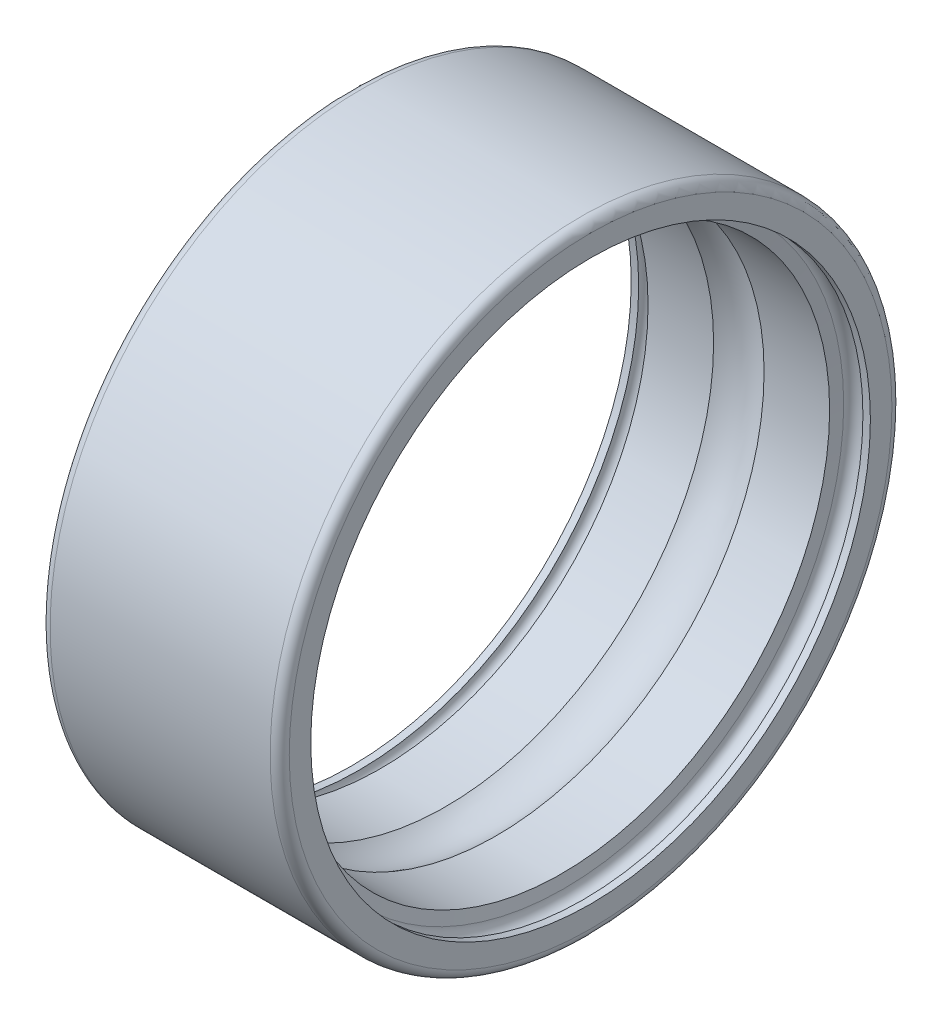
SolidWorks part; units mm, degrees
ref_plane "Front Plane" through (0, 0, 0) normal (0, 0, 1) x (1, 0, 0)
ref_plane "Top Plane" through (0, 0, 0) normal (0, 1, 0) x (1, 0, 0)
ref_plane "Right Plane" through (0, 0, 0) normal (1, 0, 0) x (0, 0, -1)
ref_plane "Plane1" through (0, 0, 0) normal (0, 0, 1) x (1, 0, 0)
sketch "Sketch1" plane through (0, 0, 0) normal (0, 0, 1) x (1, 0, 0)
  line L0 (0, 5.85) -> (0.156, 5.85)
  line L1 (0.558, 5.85) -> (0.6021, 5.6)
  line L2 (0.6021, 5.6) -> (1.9723, 5.6)
  line L3 (3.0277, 5.6) -> (4.3979, 5.6)
  line L4 (4.3979, 5.6) -> (4.442, 5.85)
  line L5 (4.844, 5.85) -> (5, 5.85)
  line L6 (5, 5.85) -> (5, 6.3)
  line L7 (4.8, 6.5) -> (0.2, 6.5)
  line L8 (0, 6.3) -> (0, 5.85)
  line L9 (4.8, 0) -> (0.2, 0) construction
  arc A0 (0.156, 5.85) -> (0.558, 5.85) centre (0.357, 5.85) cw
  arc A1 (1.9723, 5.6) -> (3.0277, 5.6) centre (2.5, 4.76) cw
  arc A2 (4.442, 5.85) -> (4.844, 5.85) centre (4.643, 5.85) cw
  arc A3 (5, 6.3) -> (4.8, 6.5) centre (4.8, 6.3) ccw
  arc A4 (0.2, 6.5) -> (0, 6.3) centre (0.2, 6.3) ccw
revolve "Revolve1" add sketch "Sketch1" angle 360 about L9
